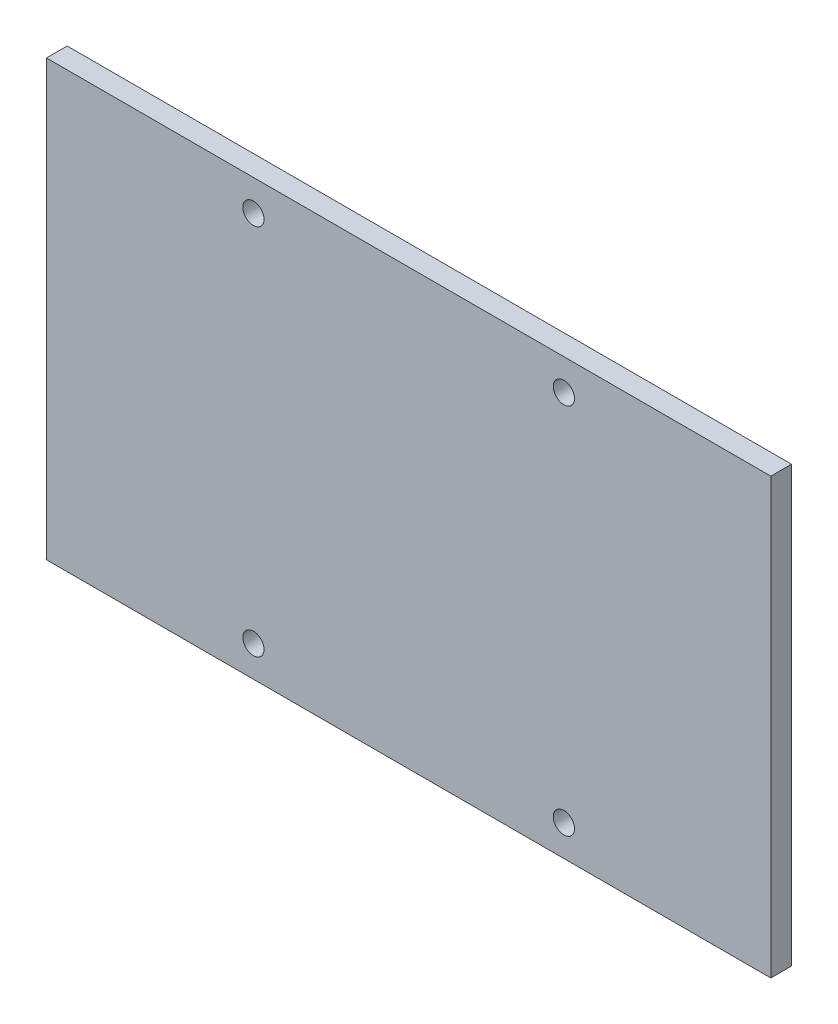
SolidWorks part; units mm, degrees
material "玻璃"
ref_plane "前视基准面" through (0, 0, 0) normal (0, 0, 1) x (1, 0, 0)
ref_plane "上视基准面" through (0, 0, 0) normal (0, 1, 0) x (1, 0, 0)
ref_plane "右视基准面" through (0, 0, 0) normal (1, 0, 0) x (0, 0, -1)
other "Configuration Table"
sketch "草图1" plane through (0, 0, 0) normal (0, 0, 1) x (1, 0, 0)
  line L1 (-15, -18) -> (15, -18) construction
  line L2 (-15, -18) -> (-15, 18) construction
  line L3 (-15, 18) -> (15, 18) construction
  line L4 (15, -18) -> (15, 18) construction
  line L5 (-15, -18) -> (15, 18) construction
  line L6 (-15, 18) -> (15, -18) construction
  line L7 (35, -21) -> (-35, -21)
  line L8 (35, -21) -> (35, 21)
  line L9 (35, 21) -> (-35, 21)
  line L10 (-35, -21) -> (-35, 21)
  line L11 (35, -21) -> (-35, 21) construction
  line L12 (35, 21) -> (-35, -21) construction
  circle A0 centre (-15, 18) radius 1.025
  circle A1 centre (15, 18) radius 1.025
  circle A2 centre (15, -18) radius 1.025
  circle A3 centre (-15, -18) radius 1.025
  point P0 (0, 0)
  point P10 (0, 0)
  dimension "D3" = 2.05
  dimension "D1" = 36
  dimension "D2" = 30
  dimension "D4" = 20
  dimension "D5" = 3
extrude "凸台-拉伸1" add sketch "草图1" along normal blind 2
